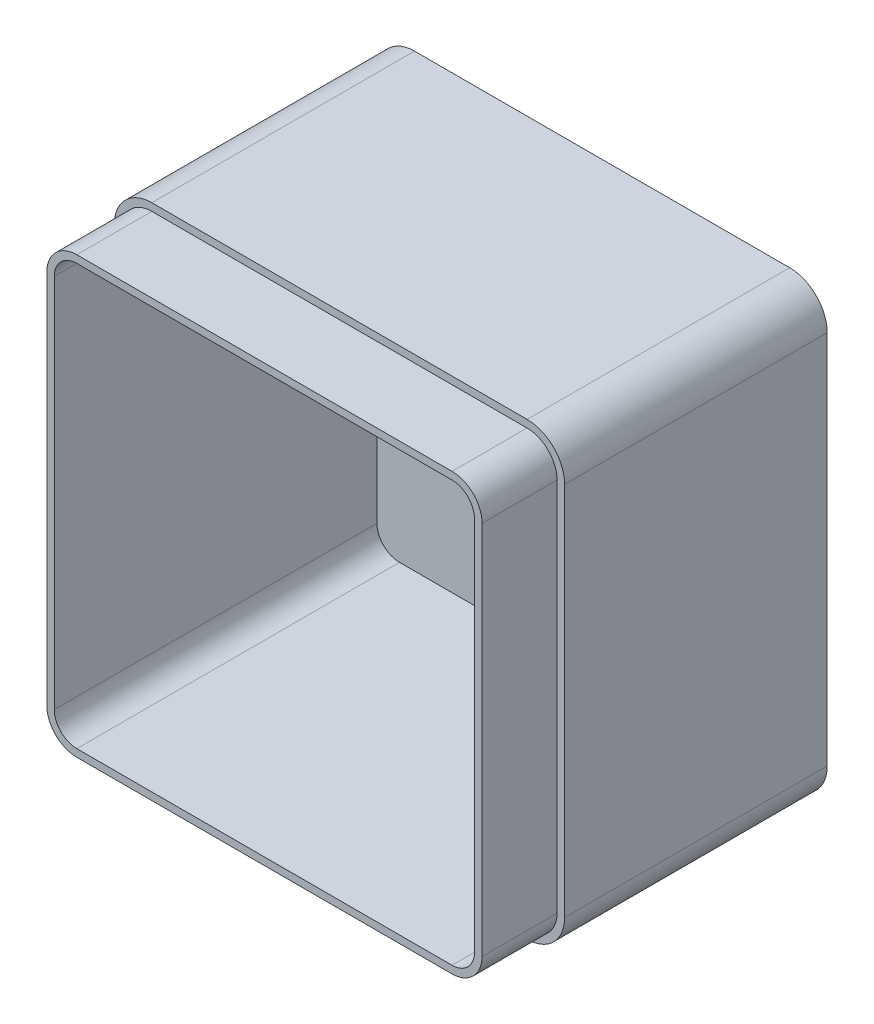
SolidWorks part; units mm, degrees
ref_plane "Front Plane" through (0, 0, 0) normal (0, 0, 1) x (1, 0, 0)
ref_plane "Top Plane" through (0, 0, 0) normal (0, 1, 0) x (1, 0, 0)
ref_plane "Right Plane" through (0, 0, 0) normal (1, 0, 0) x (0, 0, -1)
sketch "Sketch1" plane through (0, 0, 0) normal (0, 0, 1) x (1, 0, 0)
  line L1 (0, 0) -> (120, 0)
  line L2 (0, 0) -> (0, 120)
  line L3 (0, 120) -> (120, 120)
  line L4 (120, 0) -> (120, 120)
  dimension "D1" = 120
  dimension "D2" = 120
extrude "Boss-Extrude1" add sketch "Sketch1" along normal blind 90
fillet "Fillet1" radius 10 4 edges at (0, 0, 45) (120, 0, 45) (0, 120, 45) (120, 120, 45)
shell "Shell1" thickness 4
sketch "Sketch2" plane through (0, 0, 90) normal (0, 0, 1) x (1, 0, 0)
  line L4 (0, 110) -> (0, 10)
  line L5 (10, 0) -> (110, 0)
  line L6 (120, 10) -> (120, 110)
  line L7 (110, 120) -> (10, 120)
  line L8 (0, 110) -> (0, 10)
  line L9 (10, 0) -> (110, 0)
  line L10 (120, 10) -> (120, 110)
  line L11 (110, 120) -> (10, 120)
  line L16 (2, 110) -> (2, 10)
  line L17 (10, 2) -> (110, 2)
  line L18 (118, 10) -> (118, 110)
  line L19 (110, 118) -> (10, 118)
  line L20 (2, 110) -> (2, 10)
  line L21 (10, 2) -> (110, 2)
  line L22 (118, 10) -> (118, 110)
  line L23 (110, 118) -> (10, 118)
  arc A4 (0, 10) -> (10, 0) centre (10, 10) ccw
  arc A5 (110, 0) -> (120, 10) centre (110, 10) ccw
  arc A6 (120, 110) -> (110, 120) centre (110, 110) ccw
  arc A7 (10, 120) -> (0, 110) centre (10, 110) ccw
  arc A8 (0, 10) -> (10, 0) centre (10, 10) ccw
  arc A9 (110, 0) -> (120, 10) centre (110, 10) ccw
  arc A10 (120, 110) -> (110, 120) centre (110, 110) ccw
  arc A11 (10, 120) -> (0, 110) centre (10, 110) ccw
  arc A16 (2, 10) -> (10, 2) centre (10, 10) ccw
  arc A17 (110, 2) -> (118, 10) centre (110, 10) ccw
  arc A18 (118, 110) -> (110, 118) centre (110, 110) ccw
  arc A19 (10, 118) -> (2, 110) centre (10, 110) ccw
  arc A20 (2, 10) -> (10, 2) centre (10, 10) ccw
  arc A21 (110, 2) -> (118, 10) centre (110, 10) ccw
  arc A22 (118, 110) -> (110, 118) centre (110, 110) ccw
  arc A23 (10, 118) -> (2, 110) centre (10, 110) ccw
  dimension "D1" = 0
  dimension "D2" = 2
extrude "Cut-Extrude1" cut sketch "Sketch2" against normal blind 20
